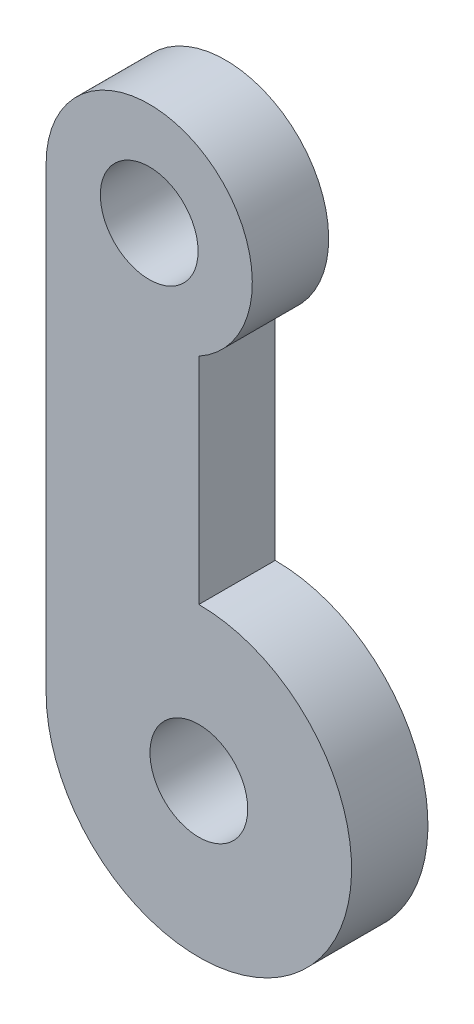
SolidWorks part; units mm, degrees
ref_plane "Front Plane" through (0, 0, 0) normal (0, 0, 1) x (1, 0, 0)
ref_plane "Top Plane" through (0, 0, 0) normal (0, 1, 0) x (1, 0, 0)
ref_plane "Right Plane" through (0, 0, 0) normal (1, 0, 0) x (0, 0, -1)
sketch "Sketch1" plane through (0, 0, 0) normal (0, 0, 1) x (1, 0, 0)
  line L0 (-3.375, -15) -> (-3.375, 0)
  line L1 (1.625, -10) -> (1.625, -2.958)
  circle A0 centre (0, 0) radius 1.6
  circle A1 centre (0, 0) radius 3.375
  circle A2 centre (1.625, -15) radius 1.6
  circle A3 centre (1.625, -15) radius 5
  dimension "D2" = 3.2
  dimension "D3" = 6.75
  dimension "D5" = 10
  dimension "D4" = 15
extrude "Boss-Extrude1" add sketch "Sketch1" along normal blind 2.5 contours A3 A2 | A3 L1 A1 L0 | A0 | A1 A0
